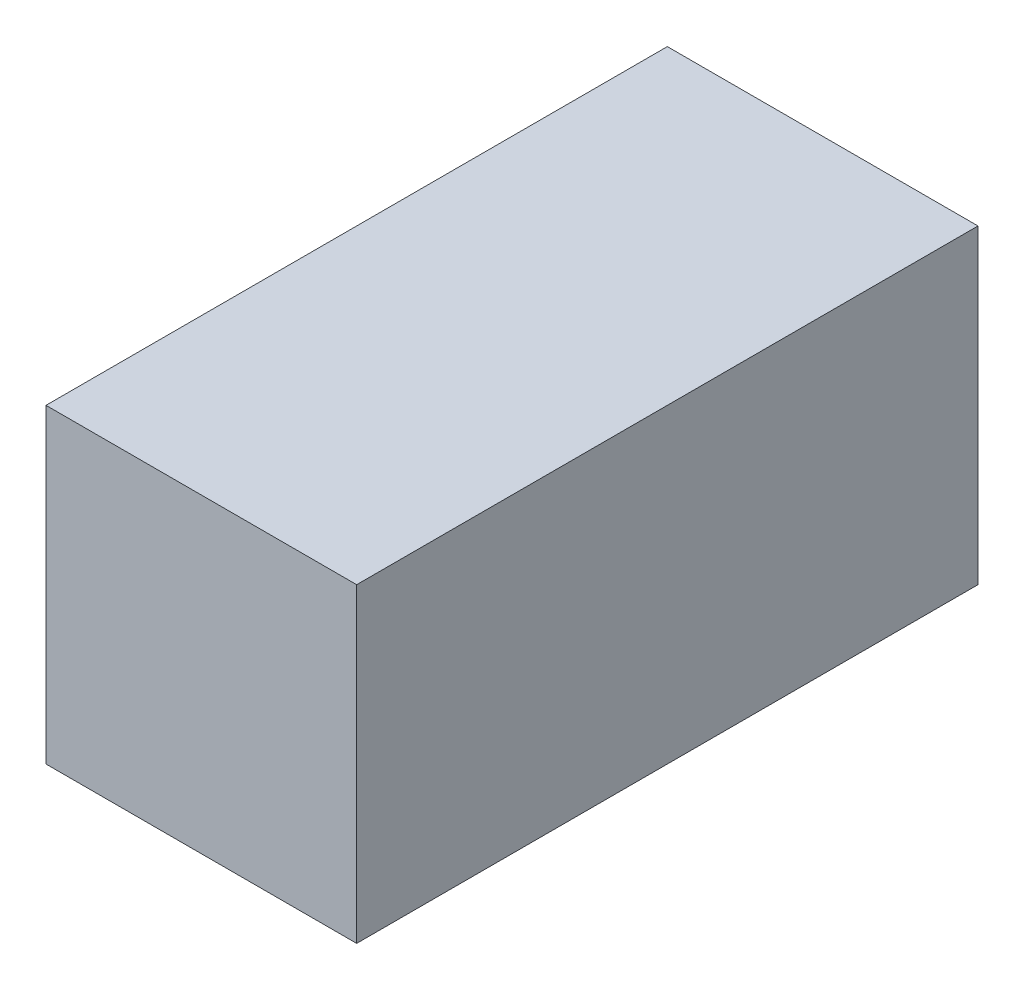
SolidWorks part; units mm, degrees
ref_plane "Front Plane" through (0, 0, 0) normal (0, 0, 1) x (1, 0, 0)
ref_plane "Top Plane" through (0, 0, 0) normal (0, 1, 0) x (1, 0, 0)
ref_plane "Right Plane" through (0, 0, 0) normal (1, 0, 0) x (0, 0, -1)
sketch "Sketch1" plane through (0, 0, 0) normal (0, 1, 0) x (1, 0, 0)
  line L1 (6, -12) -> (-6, -12)
  line L2 (6, -12) -> (6, 12)
  line L3 (6, 12) -> (-6, 12)
  line L4 (-6, -12) -> (-6, 12)
  line L5 (6, -12) -> (-6, 12) construction
  line L6 (6, 12) -> (-6, -12) construction
  point P0 (0, 0)
  dimension "D1" = 12
  dimension "D2" = 24
extrude "Boss-Extrude1" add sketch "Sketch1" along normal blind 12
